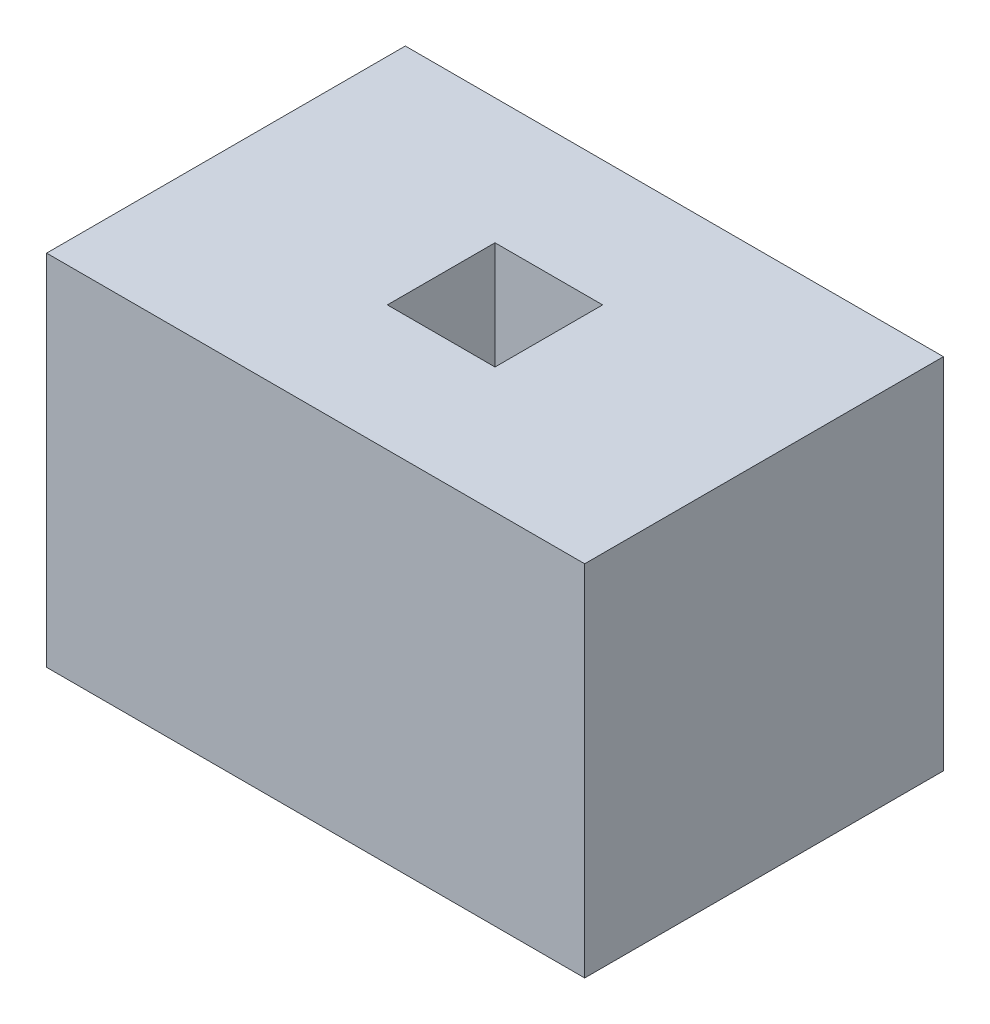
SolidWorks part; units mm, degrees
ref_plane "Front Plane" through (0, 0, 0) normal (0, 0, 1) x (1, 0, 0)
ref_plane "Top Plane" through (0, 0, 0) normal (0, 1, 0) x (1, 0, 0)
ref_plane "Right Plane" through (0, 0, 0) normal (1, 0, 0) x (0, 0, -1)
sketch "Sketch1" plane through (0, 0, 0) normal (0, 1, 0) x (1, 0, 0)
  line L1 (-1500, -1000) -> (1500, -1000)
  line L2 (-1500, -1000) -> (-1500, 1000)
  line L3 (-1500, 1000) -> (1500, 1000)
  line L4 (1500, -1000) -> (1500, 1000)
  line L5 (-1500, -1000) -> (1500, 1000) construction
  line L6 (-1500, 1000) -> (1500, -1000) construction
  point P0 (0, 0)
  dimension "D1" = 3000
  dimension "D2" = 2000
extrude "Boss-Extrude1" add sketch "Sketch1" along normal blind 2000
sketch "Sketch2" plane through (0, 0, 0) normal (0, -1, 0) x (1, 0, 0)
  line L1 (-1500, -1000) -> (1500, -1000)
  line L2 (-1500, -1000) -> (-1500, 1000)
  line L3 (-1500, 1000) -> (1500, 1000)
  line L4 (1500, -1000) -> (1500, 1000)
  line L5 (-1500, -1000) -> (1500, 1000) construction
  line L6 (-1500, 1000) -> (1500, -1000) construction
  point P0 (0, 0)
sketch "Sketch3" plane through (0, 2000, 0) normal (0, 1, 0) x (1, 0, 0)
  line L1 (-1500, 1000) -> (1500, 1000)
  line L2 (-1500, 1000) -> (-1500, -1000)
  line L3 (-1500, -1000) -> (1500, -1000)
  line L4 (1500, 1000) -> (1500, -1000)
  line L5 (-1500, 1000) -> (1500, -1000) construction
  line L6 (-1500, -1000) -> (1500, 1000) construction
  point P0 (0, 0)
  point P5 (0, 0)
sketch "Sketch4" plane through (0, 0, 1000) normal (0, 0, 1) x (1, 0, 0)
  line L0 (1500, 2000) -> (1500, 0)
  line L2 (-1500, 2000) -> (-1500, 0)
sketch "Sketch5" plane through (-1500, 0, 0) normal (-1, 0, 0) x (0, 0, 1)
  line L0 (-1000, 47.7172) -> (-1000, 2000)
  line L1 (-1000, 2000) -> (-1000, 0) construction
  line L2 (-1000, 2000) -> (-1000, 0)
  point P7 (80.4017, 7.9601)
sketch "Sketch6" plane through (0, 0, -1000) normal (0, 0, -1) x (-1, 0, 0)
  line L0 (-1500, 2000) -> (-1500, 0)
sketch "Sketch8" plane through (0, 2000, 0) normal (0, 1, 0) x (1, 0, 0)
  line L1 (-300, 300) -> (300, 300)
  line L2 (-300, 300) -> (-300, -300)
  line L3 (-300, -300) -> (300, -300)
  line L4 (300, 300) -> (300, -300)
  line L5 (-300, 300) -> (300, -300) construction
  line L6 (-300, -300) -> (300, 300) construction
  point P0 (0, 0)
  point P5 (0, 0)
  dimension "D1" = 600
  dimension "D2" = 600
extrude "Cut-Extrude1" cut sketch "Sketch8" against normal blind 600
sketch "Sketch9" plane through (0, 2000, 0) normal (0, 1, 0) x (1, 0, 0)
  line L1 (-400, 400) -> (400, 400)
  line L2 (-400, 400) -> (-400, -400)
  line L3 (-400, -400) -> (400, -400)
  line L4 (400, 400) -> (400, -400)
  line L5 (-400, 400) -> (400, -400) construction
  line L6 (-400, -400) -> (400, 400) construction
  point P0 (0, 0)
  dimension "D1" = 800
  dimension "D2" = 800
sketch3d "3DSketch1"
  line L0 (-1500, 2000, 1000) -> (-747.4301, 1331.5806, -927.3217)
  line L1 (-747.4301, 1331.5806, -927.3217) -> (-1500, 2000, -1000)
  line L2 (1500, 2000, -1000) -> (-747.4301, 1331.5806, -927.3217)
  line L3 (1500, 2000, 1000) -> (400, 1400, 400)
  line L4 (400, 2000, 400) -> (400, 1400, 400)
  line L5 (400, 2000, -400) -> (400, 1400, -400)
  line L6 (-400, 2000, 400) -> (-400, 1400, 400)
  line L7 (-400, 2000, -400) -> (-400, 1400, -400)
  line L9 (400, 1400, 400) -> (-747.4301, 1331.5806, -927.3217)
  point P21 (-143.0517, 1166.6022, -63.0122)
  point P22 (1242.603, 1782.858, -1422.9665)
  point P23 (1189.1066, 2011.8755, -1338.8309)
  point P24 (219.2833, 1839.1444, 403.6645)
  point P25 (-738.5294, 1412.4343, -880.5561)
  point P26 (-747.4301, 1331.5806, -927.3217)
  dimension "D1" = 600
  dimension "D2" = 600
  dimension "D3" = 600
  dimension "D4" = 600
